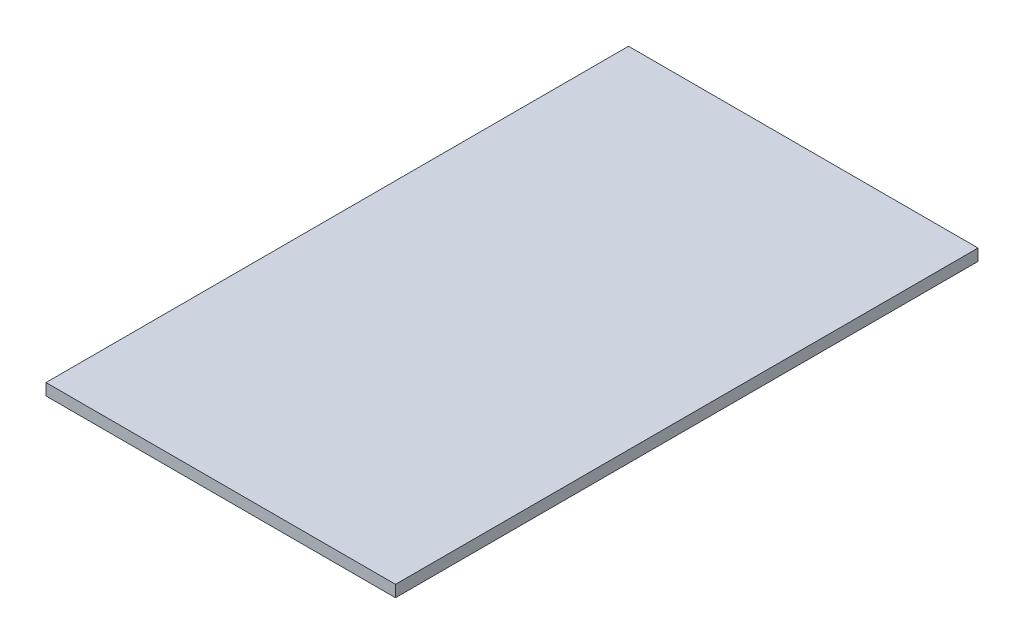
SolidWorks part; units mm, degrees
ref_plane "Front Plane" through (0, 0, 0) normal (0, 0, 1) x (1, 0, 0)
ref_plane "Top Plane" through (0, 0, 0) normal (0, 1, 0) x (1, 0, 0)
ref_plane "Right Plane" through (0, 0, 0) normal (1, 0, 0) x (0, 0, -1)
sketch "Sketch1" plane through (0, 0, 0) normal (0, 1, 0) x (1, 0, 0)
  line L1 (-30, 50) -> (30, 50)
  line L2 (-30, 50) -> (-30, -50)
  line L3 (-30, -50) -> (30, -50)
  line L4 (30, 50) -> (30, -50)
  line L5 (-30, 50) -> (30, -50) construction
  line L6 (-30, -50) -> (30, 50) construction
  point P0 (0, 0)
  dimension "D1" = 100
  dimension "D2" = 60
extrude "Boss-Extrude1" add sketch "Sketch1" along normal blind 2
